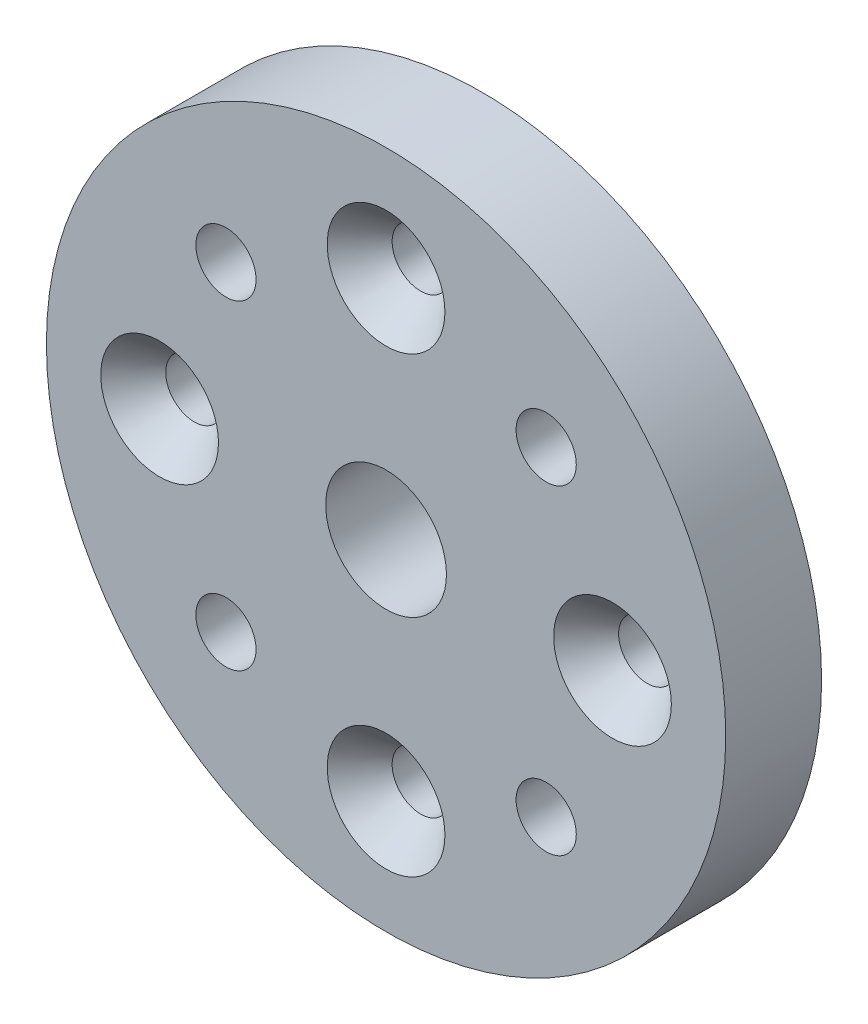
SolidWorks part; units mm, degrees
material "Balsa"
ref_plane "Front Plane" through (0, 0, 0) normal (0, 0, 1) x (1, 0, 0)
ref_plane "Top Plane" through (0, 0, 0) normal (0, 1, 0) x (1, 0, 0)
ref_plane "Right Plane" through (0, 0, 0) normal (1, 0, 0) x (0, 0, -1)
sketch "Sketch1" plane through (0, 0, 0) normal (0, 0, 1) x (1, 0, 0)
  circle A0 centre (0, 0) radius 22.5
  circle A1 centre (0, 0) radius 4
  circle A2 centre (0, 0) radius 15 construction
  circle A3 centre (0, 15) radius 1.8986
  circle A4 centre (10.6066, 10.6066) radius 1.9939
  circle A5 centre (15, 0) radius 1.8986
  circle A6 centre (10.6066, -10.6066) radius 1.9939
  circle A7 centre (0, -15) radius 1.8986
  circle A8 centre (-10.6066, -10.6066) radius 1.9939
  circle A9 centre (-15, 0) radius 1.8986
  circle A10 centre (-10.6066, 10.6066) radius 1.9939
  dimension "D1" = 45
  dimension "D2" = 8
  dimension "D3" = 30
  dimension "D4" = 3.7973
  dimension "D5" = 3.9878
  dimension "D6" = 45
  dimension "D7" = 4
extrude "Boss-Extrude1" add sketch "Sketch1" along normal blind 6.35
other "Move Face1" [suppressed] parameters "D1"=0.08
chamfer "Chamfer1" distance 2.301 angle 41 4 edges at (1.8987, -15, 6.35) (-13.1014, 0, 6.35) (1.8986, 15, 6.35) (16.8986, 0, 6.35)
